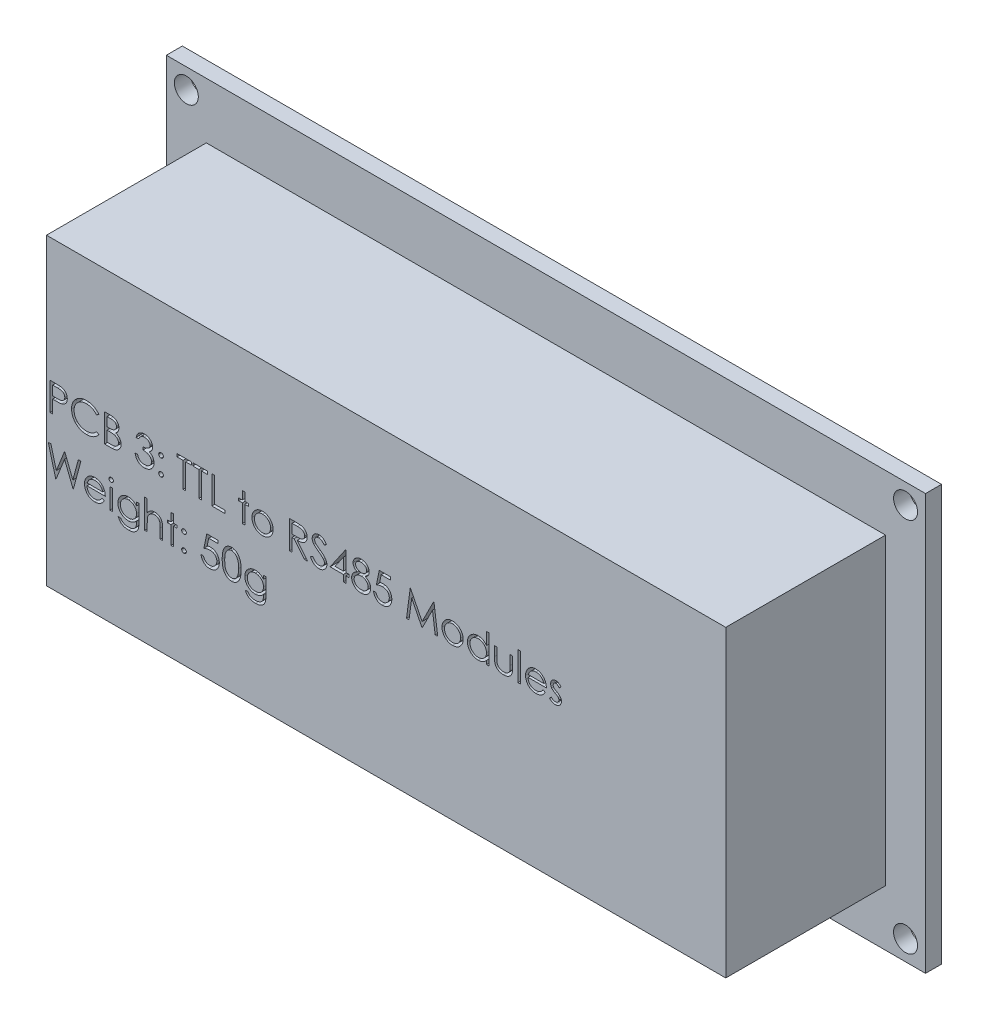
SolidWorks part; units mm, degrees
ref_plane "Front Plane" through (0, 0, 0) normal (0, 0, 1) x (1, 0, 0)
ref_plane "Top Plane" through (0, 0, 0) normal (0, 1, 0) x (1, 0, 0)
ref_plane "Right Plane" through (0, 0, 0) normal (1, 0, 0) x (0, 0, -1)
sketch "Sketch1" plane through (0, 0, 0) normal (0, 0, 1) x (1, 0, 0)
  line L0 (-47.5, 26) -> (47.5, 26)
  line L1 (-47.5, 26) -> (-47.5, -26)
  line L2 (-47.5, -26) -> (47.5, -26)
  line L3 (47.5, 26) -> (47.5, -26)
  line L4 (0, -26) -> (0, 26) construction
  line L5 (-47.5, 0) -> (47.5, 0) construction
  line L6 (-45, -23.5) -> (45, -23.5)
  line L7 (-45, -23.5) -> (-45, 23.5)
  line L8 (-45, 23.5) -> (45, 23.5)
  line L9 (45, -23.5) -> (45, 23.5)
  line L10 (-45, -23.5) -> (45, 23.5) construction
  line L11 (-45, 23.5) -> (45, -23.5) construction
  circle A0 centre (-45, 23.5) radius 1.5
  circle A1 centre (-45, -23.5) radius 1.5
  circle A2 centre (45, -23.5) radius 1.5
  circle A3 centre (45, 23.5) radius 1.5
  point P4 (0, 0)
  point P17 (0, 0)
  dimension "D5" = 3
  dimension "D6" = 3
  dimension "D7" = 3
  dimension "D8" = 3
  dimension "D1" = 52
  dimension "D2" = 95
  dimension "D3" = 2.5
  dimension "D4" = 2.5
extrude "Boss-Extrude1" add sketch "Sketch1" along normal blind 2 contours A3 L8 A0 L7 A1 L6 A2 L9 | L3 L0 L1 L2 A3 L9 A2 L6 A1 L7 A0 L8
sketch "Sketch2" plane through (0, 0, 2) normal (0, 0, 1) x (1, 0, 0)
  line L0 (-47.5, 26) -> (47.5, 26) construction
  line L1 (-42.5, -19) -> (42.5, -19)
  line L2 (-42.5, -19) -> (-42.5, 19)
  line L3 (-42.5, 19) -> (42.5, 19)
  line L4 (42.5, -19) -> (42.5, 19)
  line L5 (-42.5, -19) -> (42.5, 19) construction
  line L6 (-42.5, 19) -> (42.5, -19) construction
  line L7 (-47.5, 26) -> (-47.5, -26) construction
  point P0 (0, 0)
  dimension "D1" = 7
  dimension "D2" = 5
extrude "Boss-Extrude2" add sketch "Sketch2" along normal blind 20
sketch "Sketch3" plane through (0, 0, 22) normal (0, 0, 1) x (1, 0, 0)
  line L0 (-42.5, 0) -> (42.5, 0) construction
  line L1 (-42.5, 19) -> (-42.5, -19) construction
  line L2 (42.5, -19) -> (42.5, 19) construction
  text T0 "PCB 3: TTL to RS485 Modules\r\nWeight: 50g"
  dimension "D1" = 42.5
  dimension "D2" = 42.5
extrude "Cut-Extrude1" cut sketch "Sketch3" against normal blind 2
